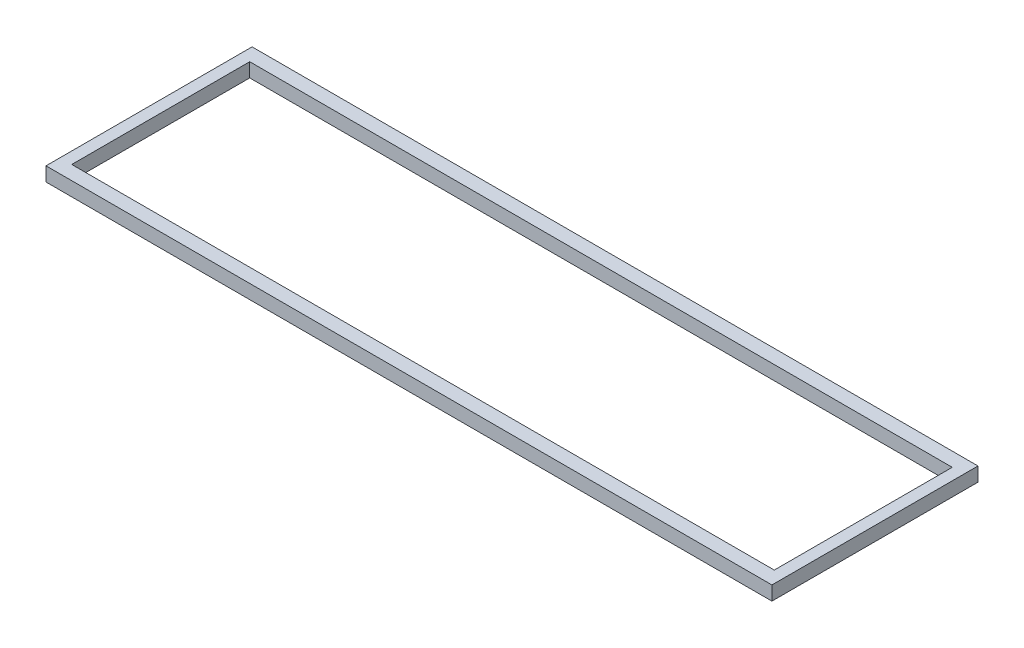
SolidWorks part; units mm, degrees
ref_plane "Front Plane" through (0, 0, 0) normal (0, 0, 1) x (1, 0, 0)
ref_plane "Top Plane" through (0, 0, 0) normal (0, 1, 0) x (1, 0, 0)
ref_plane "Right Plane" through (0, 0, 0) normal (1, 0, 0) x (0, 0, -1)
sketch "Sketch1" plane through (0, 0, 0) normal (0, 1, 0) x (1, 0, 0)
  line L1 (-775, 341.4243) -> (775, 341.4243)
  line L2 (-775, 341.4243) -> (-775, -98.5757)
  line L3 (-775, -98.5757) -> (775, -98.5757)
  line L4 (775, 341.4243) -> (775, -98.5757)
  line L5 (-750, 311.4243) -> (750, 311.4243)
  line L6 (-750, 311.4243) -> (-750, -68.5757)
  line L7 (-750, -68.5757) -> (750, -68.5757)
  line L8 (750, 311.4243) -> (750, -68.5757)
  point P8 (0, 311.4243)
  point P10 (0, 341.4243)
  dimension "D1" = 1550
  dimension "D2" = 1500
  dimension "D3" = 440
  dimension "D4" = 380
  dimension "D5" = 30
  dimension "D6" = 30
extrude "Boss-Extrude1" add sketch "Sketch1" along normal blind 30
